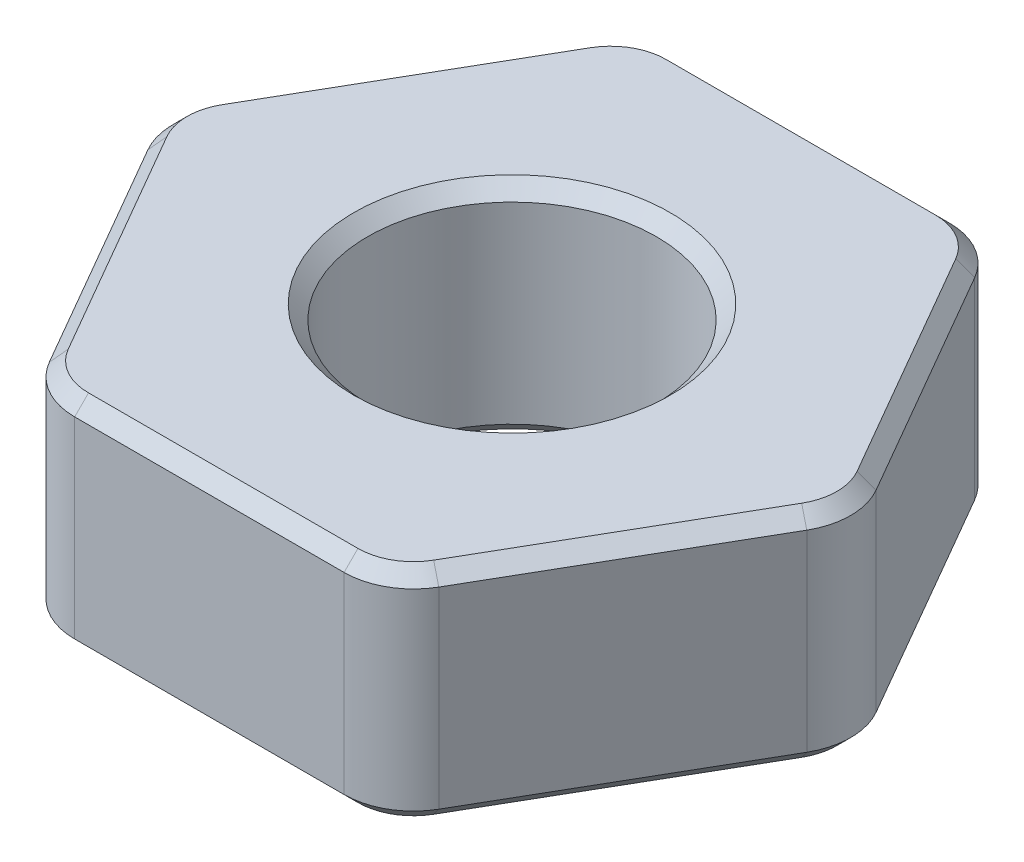
SolidWorks part; units mm, degrees
ref_plane "Front" through (0, 0, 0) normal (0, 0, 1) x (1, 0, 0)
ref_plane "Top" through (0, 0, 0) normal (0, 1, 0) x (1, 0, 0)
ref_plane "Right" through (0, 0, 0) normal (1, 0, 0) x (0, 0, -1)
sketch "Sketch1" plane through (0, 0, 0) normal (0, 1, 0) x (1, 0, 0)
  line L1 (2.5205, 4.3656) -> (-2.5205, 4.3656)
  line L2 (-2.5205, 4.3656) -> (-5.041, 0)
  line L3 (-5.041, 0) -> (-2.5205, -4.3656)
  line L4 (-2.5205, -4.3656) -> (2.5205, -4.3656)
  line L5 (2.5205, -4.3656) -> (5.041, 0)
  line L6 (5.041, 0) -> (2.5205, 4.3656)
  circle A0 centre (0, 0) radius 4.3656 construction
  circle A1 centre (0, 0) radius 2.0828
  dimension "D2" = 4.1656
  dimension "D1" = 8.7312
extrude "Boss-Extrude1" add sketch "Sketch1" along normal mid plane 3.175 contours L2 L3 L4 L5 L6 L1
fillet "Fillet1" radius 1 6 edges at (5.041, 0, 0) (2.5205, 0, 4.3656) (-5.041, 0, 0) (-2.5205, 0, -4.3656) (2.5205, 0, -4.3656) (-2.5205, 0, 4.3656)
chamfer "Chamfer1" distance 0.2 angle 45 26 edges at (0, -1.5875, 2.0828) (2.4431, -1.5875, -4.2317) (0, -1.5875, -4.3656) (-2.4431, -1.5875, -4.2317) (-3.7807, -1.5875, -2.1828) (-4.8863, -1.5875, 0) (-3.7807, -1.5875, 2.1828) (-2.4431, -1.5875, 4.2317) (0, -1.5875, 4.3656) (2.4431, -1.5875, 4.2317) (3.7807, -1.5875, 2.1828) (4.8863, -1.5875, 0) (3.7807, -1.5875, -2.1828) (0, 1.5875, 2.0828) (2.4431, 1.5875, 4.2317) (0, 1.5875, 4.3656) (-2.4431, 1.5875, 4.2317) (-3.7807, 1.5875, 2.1828) (-4.8863, 1.5875, 0) (-3.7807, 1.5875, -2.1828) (-2.4431, 1.5875, -4.2317) (0, 1.5875, -4.3656) (2.4431, 1.5875, -4.2317) (3.7807, 1.5875, -2.1828) (4.8863, 1.5875, 0) (3.7807, 1.5875, 2.1828)
